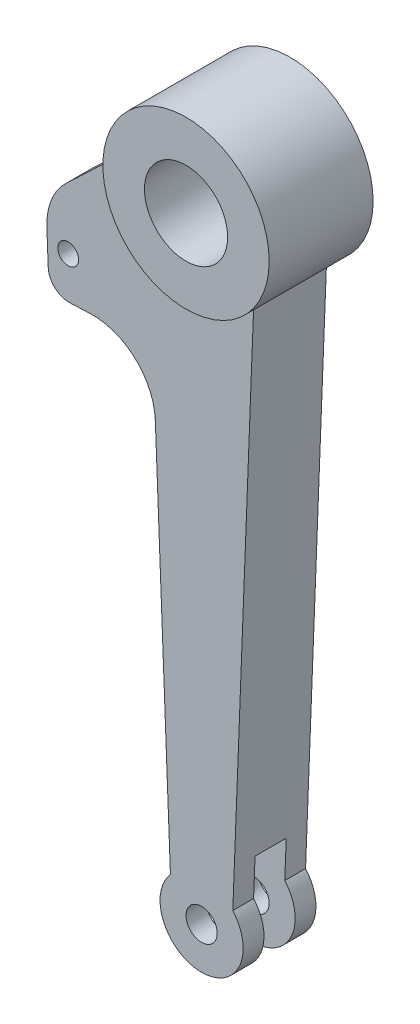
SolidWorks part; units mm, degrees
ref_plane "Front Plane" through (0, 0, 0) normal (0, 0, 1) x (1, 0, 0)
ref_plane "Top Plane" through (0, 0, 0) normal (0, 1, 0) x (1, 0, 0)
ref_plane "Right Plane" through (0, 0, 0) normal (1, 0, 0) x (0, 0, -1)
sketch "Sketch1" plane through (0, 0, 0) normal (0, 0, 1) x (1, 0, 0)
  circle A0 centre (0, 0) radius 40
  circle A1 centre (0, 0) radius 20
  dimension "D1" = 80
  dimension "D2" = 40
extrude "Boss-Extrude1" add sketch "Sketch1" along normal mid plane 50
sketch "Sketch3" plane through (0, 0, 0) normal (0, 0, 1) x (1, 0, 0)
  line L0 (-25, -31.225) -> (-15, -286.7712)
  line L1 (-20, -300) -> (20, -300) construction
  line L2 (15, -286.7712) -> (25, -31.225)
  line L3 (-25, -31.225) -> (0, -31.225) construction
  line L4 (0, -31.225) -> (25, -31.225) construction
  line L5 (0, -31.225) -> (0, 0) construction
  line L6 (-15, -286.7712) -> (15, -286.7712) construction
  circle A0 centre (0, 0) radius 40 construction
  arc A1 (-25, -31.225) -> (25, -31.225) centre (0, 0) ccw
  arc A2 (-15, -286.7712) -> (15, -286.7712) centre (0, -300) ccw
  circle A3 centre (0, -300) radius 7.5
  dimension "D1" = 50
  dimension "D4" = 40
  dimension "D5" = 15
  dimension "D2" = 40
  dimension "D3" = 300
  dimension "D6" = 30
extrude "Boss-Extrude3" add sketch "Sketch3" along normal mid plane 35
sketch "Sketch5" plane through (0, 0, 0) normal (0, 0, 1) x (1, 0, 0)
  circle A0 centre (0, -300) radius 35
  dimension "D1" = 70
extrude "Cut-Extrude1" cut sketch "Sketch5" against normal mid plane 15
sketch "Sketch6" plane through (-26.1818, -1.0245, 0) normal (-0.9992, -0.0391, 0) x (0, 0, 1)
  line L0 (0, 0) -> (0, -267.9024) construction
  line L1 (-7.5, -267.9024) -> (7.5, -267.9024) construction
  line L2 (17.5, -30.2236) -> (17.5, -285.9654) construction
  line L3 (-17.5, -30.2236) -> (17.5, -30.2236)
  line L4 (-17.5, -30.2236) -> (-17.5, -70.2236)
  line L5 (-17.5, -70.2236) -> (17.5, -70.2236)
  line L6 (17.5, -30.2236) -> (17.5, -70.2236)
  line L7 (-17.5, -30.2236) -> (17.5, -70.2236) construction
  line L8 (-17.5, -70.2236) -> (17.5, -30.2236) construction
  line L9 (17.5, -30.2236) -> (-17.5, -30.2236) construction
  line L10 (5, -30.2236) -> (5, -70.2236)
  line L11 (-5, -30.2236) -> (-5, -70.2236)
  line L12 (5, -50.2236) -> (0, -50.2236) construction
  line L13 (0, -50.2236) -> (-5, -50.2236) construction
  point P5 (0, -50.2236)
  line M11 (17.5, -285.9654) -> (17.5, -30.2236)
  line M12 (17.5, -30.2236) -> (-17.5, -30.2236)
  line M13 (-17.5, -30.2236) -> (-17.5, -285.9654)
  dimension "D1" = 40
  dimension "D2" = 10
extrude "Boss-Extrude4" add sketch "Sketch6" along normal blind 50 contours L10 L5 M12 M11 | L11 L5 M12 M13
sketch "Sketch7" plane through (0, 0, -17.5) normal (0, 0, -1) x (-1, 0, 0)
  line L0 (74.9618, -33.1801) -> (53.413, -72.3675) construction
  line L1 (73.3977, -73.1495) -> (23.4359, -71.1944) construction
  line L2 (74.9618, -33.1801) -> (73.3977, -73.1495) construction
  circle A0 centre (64.1874, -52.7738) radius 5
  point P6 (52.6552, -72.3378)
  dimension "D1" = 10
  dimension "D2" = 10
extrude "Cut-Extrude2" cut sketch "Sketch7" against normal through all
sketch "Sketch8" plane through (0, 0, -17.5) normal (0, 0, -1) x (-1, 0, 0)
  line L0 (74.9618, -33.1801) -> (40, 0)
  line L1 (25, -31.225) -> (74.9618, -33.1801)
  line L2 (0, 0) -> (40, 0) construction
  circle A0 centre (0, 0) radius 40 construction
  arc A1 (40, 0) -> (25, -31.225) centre (0, 0) cw
extrude "Boss-Extrude5" add sketch "Sketch8" against normal blind 12.5
mirror "Mirror2" about plane through (0, 0, 0) normal (0, 0, 1) of "Boss-Extrude5"
fillet "Fillet2" radius 10 2 edges at (-73.3977, -73.1495, -11.25) (-73.3977, -73.1495, 11.25)
fillet "Fillet3" radius 30 2 edges at (-23.4359, -71.1944, 11.25) (-23.4359, -71.1944, -11.25)
fillet "Fillet4" radius 10 2 edges at (-40, 0, 11.25) (-40, 0, -11.25)
fillet "Fillet5" radius 30 2 edges at (-74.9618, -33.1801, 11.25) (-74.9618, -33.1801, -11.25)
